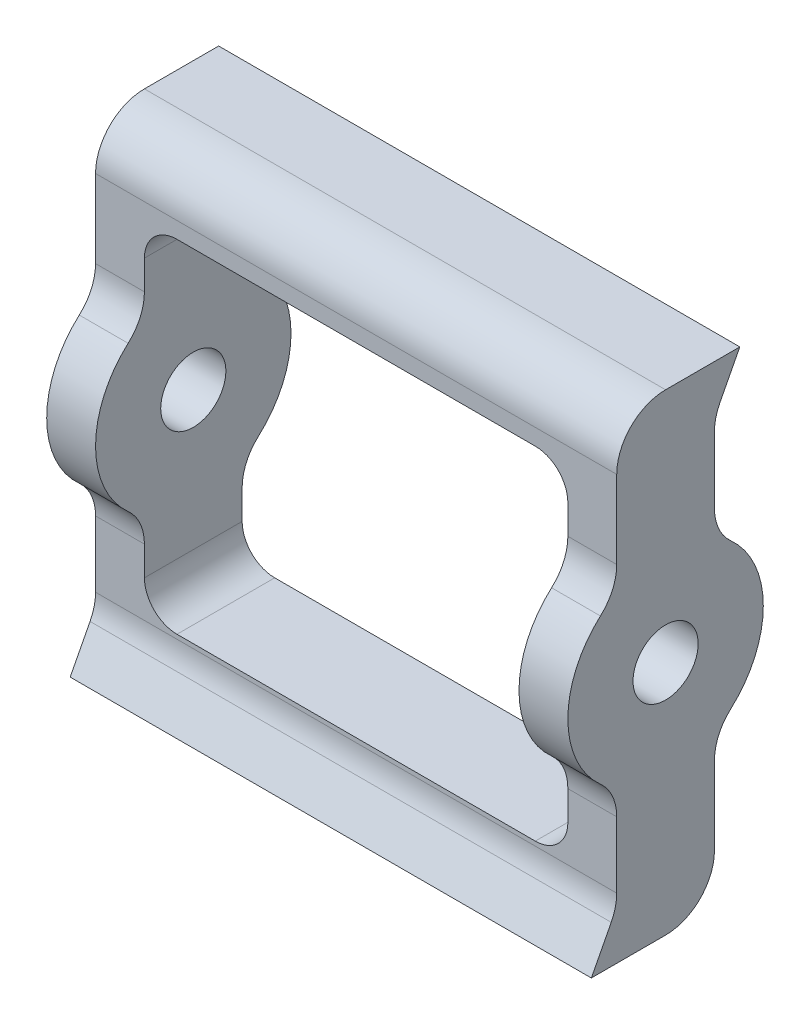
SolidWorks part; units mm, degrees
material "AISI Type A2 Tool Steel"
ref_plane "Front Plane" through (0, 0, 0) normal (0, 0, 1) x (1, 0, 0)
ref_plane "Top Plane" through (0, 0, 0) normal (0, 1, 0) x (1, 0, 0)
ref_plane "Right Plane" through (0, 0, 0) normal (1, 0, 0) x (0, 0, -1)
other "Bounding Box"
ref_plane "Default Plane" through (-8.9266, -12.7485, 0) normal (-0.1736, 0.9848, 0) x (0.9848, 0.1736, 0)
sketch "Sketch1" plane through (0, 0, 0) normal (1, 0, 0) x (0, 0, -1)
  line L0 (9.525, 36.5125) -> (14.4733, 46.0375)
  line L1 (-9.525, -36.5125) -> (9.525, -36.5125) construction
  line L2 (-9.525, -36.5125) -> (-9.525, -16.4978)
  line L3 (-9.525, 36.5125) -> (9.525, 36.5125) construction
  line L4 (9.525, -36.5125) -> (9.525, -16.4978)
  line L5 (-9.525, -36.5125) -> (9.525, 36.5125) construction
  line L6 (-9.525, 36.5125) -> (9.525, -36.5125) construction
  line L7 (14.4733, 46.0375) -> (-9.525, 46.0375)
  line L8 (-9.525, 46.0375) -> (-9.525, 36.5125)
  line L9 (9.525, -36.5125) -> (9.525, -46.0375)
  line L10 (9.525, -46.0375) -> (-14.4733, -46.0375)
  line L11 (-14.4733, -46.0375) -> (-9.525, -36.5125)
  line L12 (-14.4733, -46.0375) -> (0, 0) construction
  line L13 (-9.525, 16.4978) -> (-9.525, 36.5125)
  line L14 (9.525, 16.4978) -> (9.525, 36.5125)
  circle A0 centre (0, 0) radius 6.35
  arc A1 (-9.525, 16.4978) -> (-9.525, -16.4978) centre (0, 0) ccw
  arc A2 (9.525, -16.4978) -> (9.525, 16.4978) centre (0, 0) ccw
  point P0 (0, 0)
  point P13 (9.525, 36.3558)
  dimension "D5" = 12.7
  dimension "D6" = 38.1
  dimension "D1" = 92.075
  dimension "D2" = 19.05
  dimension "D3" = 10
  dimension "D4" = 9.525
extrude "Boss-Extrude1" add sketch "Sketch1" along normal mid plane 101.6
sketch "Sketch2" plane through (0, 0, 0) normal (0, 0, 1) x (1, 0, 0)
  line L0 (50.8, 46.0375) -> (-50.8, 46.0375) construction
  line L1 (-41.275, -33.3375) -> (41.275, -33.3375)
  line L2 (-41.275, -33.3375) -> (-41.275, 33.3375)
  line L3 (-41.275, 33.3375) -> (41.275, 33.3375)
  line L4 (41.275, -33.3375) -> (41.275, 33.3375)
  line L5 (-41.275, -33.3375) -> (41.275, 33.3375) construction
  line L6 (-41.275, 33.3375) -> (41.275, -33.3375) construction
  line L7 (-50.8, 46.0375) -> (-50.8, 16.4978) construction
  point P0 (0, 0)
  dimension "D1" = 12.7
  dimension "D2" = 9.525
extrude "Cut-Extrude1" cut sketch "Sketch2" against normal through all both and the other way through all
fillet "Fillet1" radius 6.35 4 edges at (-41.275, 33.3375, 0) (41.275, 33.3375, 0) (41.275, -33.3375, 0) (-41.275, -33.3375, 0)
fillet "Fillet2" radius 9.525 8 edges at (-46.0375, 16.4978, -9.525) (-46.0375, -16.4978, -9.525) (46.0375, 16.4978, -9.525) (46.0375, -16.4978, -9.525) (-46.0375, 16.4978, 9.525) (-46.0375, -16.4978, 9.525) (46.0375, -16.4978, 9.525) (46.0375, 16.4978, 9.525)
fillet "Fillet3" radius 9.525 2 edges at (0, -46.0375, -9.525) (0, 46.0375, 9.525)
fillet "Fillet4" radius 9.525 2 edges at (0, 36.5125, -9.525) (0, -36.5125, 9.525)
